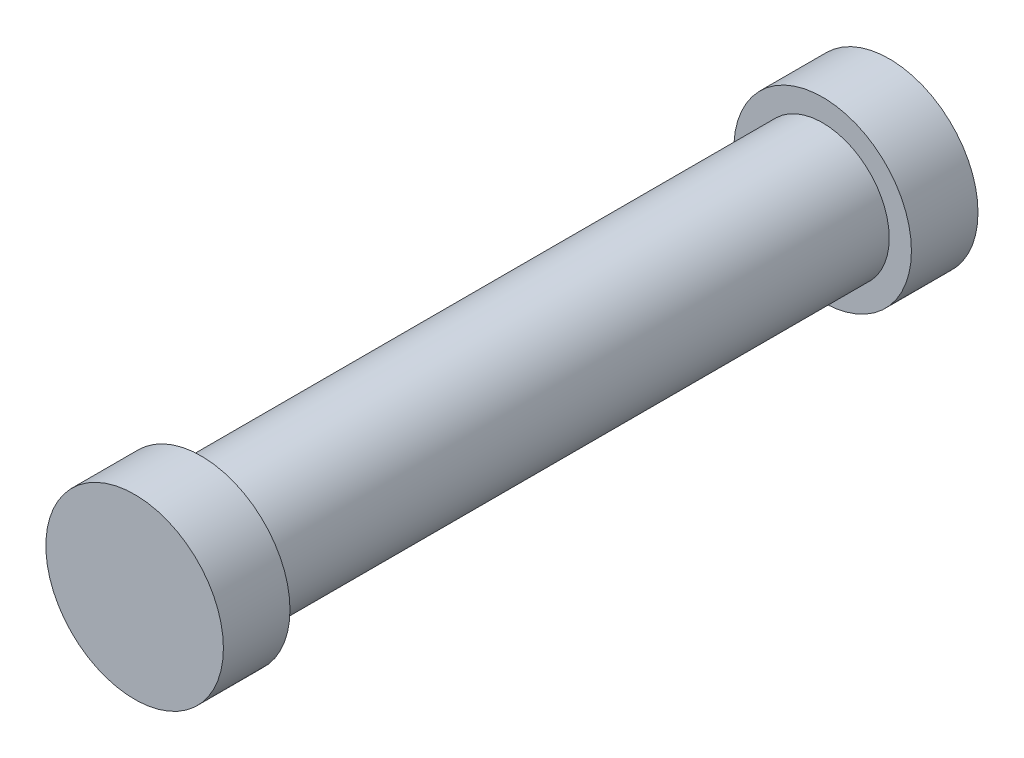
SolidWorks part; units mm, degrees
ref_plane "Front Plane" through (0, 0, 0) normal (0, 0, 1) x (1, 0, 0)
ref_plane "Top Plane" through (0, 0, 0) normal (0, 1, 0) x (1, 0, 0)
ref_plane "Right Plane" through (0, 0, 0) normal (1, 0, 0) x (0, 0, -1)
sketch "Sketch1" plane through (0, 0, 0) normal (0, 0, 1) x (1, 0, 0)
  circle A0 centre (0, 0) radius 25.4
  dimension "D1" = 50.8
extrude "Boss-Extrude1" add sketch "Sketch1" along normal blind 19.05
sketch "Sketch2" plane through (0, 0, 19.05) normal (0, 0, 1) x (1, 0, 0)
  circle A0 centre (0, 0) radius 19.05
  dimension "D1" = 38.1
extrude "Boss-Extrude3" add sketch "Sketch2" along normal blind 177.8
sketch "Sketch4" plane through (0, 0, 196.85) normal (0, 0, 1) x (1, 0, 0)
  circle A0 centre (0, 0) radius 25.4
extrude "Boss-Extrude4" add sketch "Sketch4" along normal blind 19.05
